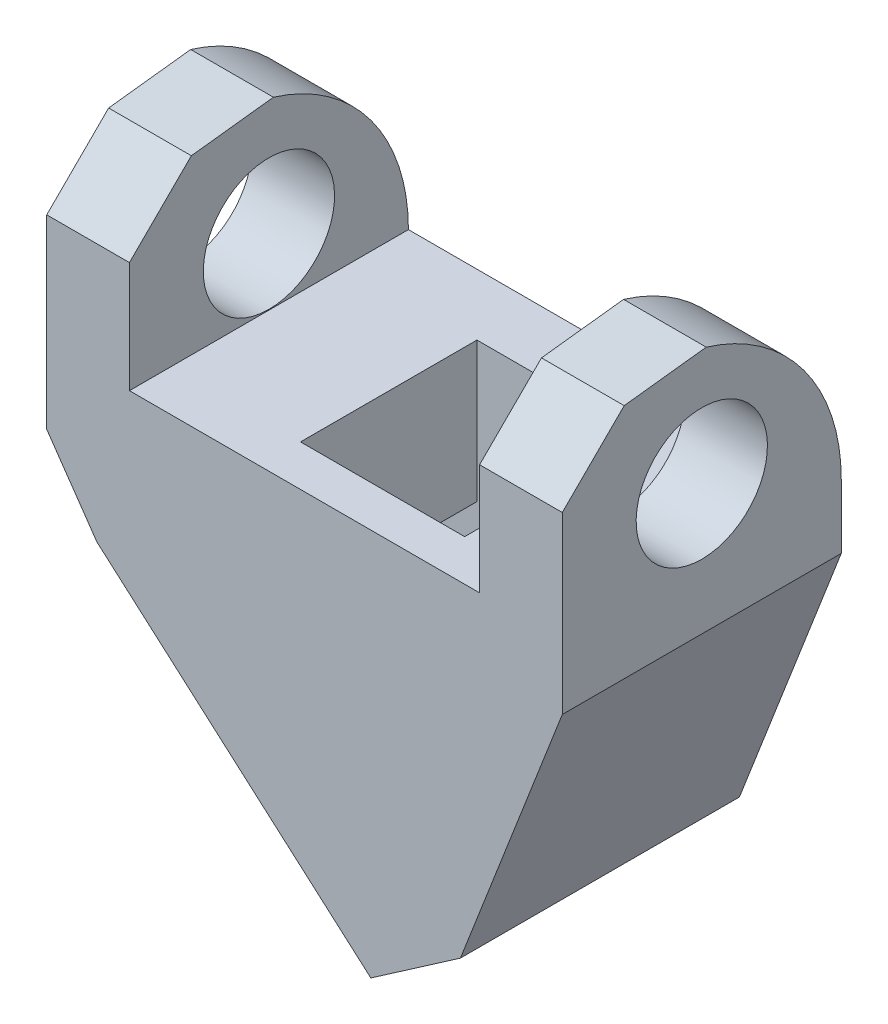
SolidWorks part; units mm, degrees
ref_plane "Plan de face" through (0, 0, 0) normal (0, 0, 1) x (1, 0, 0)
ref_plane "Plan de dessus" through (0, 0, 0) normal (0, 1, 0) x (1, 0, 0)
ref_plane "Plan de droite" through (0, 0, 0) normal (1, 0, 0) x (0, 0, -1)
sketch "Sketch1" plane through (0, 0, 0) normal (0, 0, 1) x (1, 0, 0)
  line L0 (0, 0) -> (0, 11.1)
  line L1 (0, 11.1) -> (5.04, 11.1)
  line L2 (5.04, 11.1) -> (5.04, -3.9)
  line L3 (5.04, -3.9) -> (-1.1665, -19.86)
  line L4 (-1.1665, -19.86) -> (-6.6262, -23.6391)
  line L5 (-6.6262, -23.6391) -> (-23.3193, -8.9738)
  line L6 (-23.3193, -8.9738) -> (-26.3756, -4.5584)
  line L7 (-26.3756, -4.5584) -> (-26.3756, 11.1)
  line L8 (-26.3756, 11.1) -> (-21.3356, 11.1)
  line L9 (-21.3356, 11.1) -> (-21.3356, 0)
  line L10 (-21.3356, 0) -> (0, 0)
  dimension "D1" = 5.04
  dimension "D2" = 5.04
  dimension "D3" = 15
  dimension "D4" = 158.75
  dimension "D5" = 15.96
  dimension "D6" = 6.64
  dimension "D7" = 145.94
  dimension "D8" = 104.01
  dimension "D9" = 22.22
  dimension "D10" = 5.37
  dimension "D11" = 21.3356
  dimension "D12" = 11.1
extrude "Boss-Extrude1" add sketch "Sketch1" along normal blind 17
sketch "Sketch2" plane through (0, 0, 0) normal (-1, 0, 0) x (0, 0, 1)
  line L2 (17, 0) -> (17, 6.76)
  line L3 (17, 11.1) -> (17, 0) construction
  line L4 (17, 6.76) -> (13.2281, 10.5122)
  line L6 (13.2281, 10.5122) -> (8.2281, 11.1)
  line L7 (17, 11.1) -> (0, 11.1) construction
  line L9 (0, 11.1) -> (0, 0) construction
  line L10 (17, 6.76) -> (17, 12.8811)
  line L12 (0, 12.8811) -> (0, 0)
  line L13 (0, 12.8811) -> (17, 12.8811)
  arc A0 (8.2281, 11.1) -> (0, 0) centre (11.6012, 0) ccw
  line M6 (0, 11.1) -> (0, 0)
  line M8 (17, 0) -> (17, 11.1)
  line M9 (17, 11.1) -> (0, 11.1)
  dimension "D1" = 6.76
  dimension "D2" = 134.85
  dimension "D3" = 5
  dimension "D4" = 10
extrude "Cut-Extrude1" cut sketch "Sketch2" against normal mid plane 62 contours L13 L12 L10 M9 | A0 M9 M6 | L6 L4 M8 M9
ref_plane "Plane1" through (0, 0, 7) normal (0, 0, 1) x (1, 0, 0)
sketch "Sketch3" plane through (-14.6075, -16.6273, 0) normal (-0.66, -0.7513, 0) x (-0.7513, 0.66, 0)
  line L0 (-10.6238, -17) -> (-10.6238, 0) construction
  line L1 (5.8662, -3.74) -> (-6.6038, -3.74)
  line L2 (5.8662, -3.74) -> (5.8662, -14.49)
  line L3 (5.8662, -14.49) -> (-6.6038, -14.49)
  line L4 (-6.6038, -3.74) -> (-6.6038, -14.49)
  line L5 (11.5962, 0) -> (-10.6238, 0) construction
  dimension "D1" = 10.75
  dimension "D2" = 12.47
  dimension "D3" = 4.02
  dimension "D4" = 3.74
sketch "Sketch5" plane through (0, 0, 7) normal (0, 0, 1) x (1, 0, 0)
  line L0 (-11.0796, -19.7266) -> (-3.7738, -14.2012)
  line L1 (-19.0145, -12.7556) -> (-9.6463, -20.9859) construction
  dimension "D1" = 101.6
  dimension "D2" = 9.16
sweep "Cut-Sweep1" cut profiles "Sketch3" path "Sketch5"
sketch "Sketch6" plane through (0, 0, 0) normal (0, 1, 0) x (1, 0, 0)
  line L0 (5.04, -13.2281) -> (5.04, -8.2281) construction
  line L1 (-3.42, -14.49) -> (-13.42, -14.49)
  line L2 (-3.42, -14.49) -> (-3.42, -3.74)
  line L3 (-3.42, -3.74) -> (-13.42, -3.74)
  line L4 (-13.42, -14.49) -> (-13.42, -3.74)
  line L5 (0, 0) -> (-21.3356, 0) construction
  dimension "D1" = 10.75
  dimension "D2" = 10
  dimension "D3" = 8.46
  dimension "D4" = 3.74
extrude "Cut-Extrude2" cut sketch "Sketch6" against normal up to surface (23.8399 mm away)
ref_plane "Plane2" through (-10.6678, 0, 0) normal (-1, 0, 0) x (0, 0, 1)
sketch "Sketch7" plane through (-10.6678, 0, 0) normal (-1, 0, 0) x (0, 0, 1)
  line L0 (17, -4.5584) -> (0, -4.5584) construction
  line L1 (17, 6.76) -> (17, -4.5584) construction
  circle A0 centre (8.5, 4.0416) radius 4
  dimension "D2" = 8
  dimension "D1" = 8.6
  dimension "D3" = 8.5
extrude "Cut-Extrude3" cut sketch "Sketch7" against normal mid plane 62
